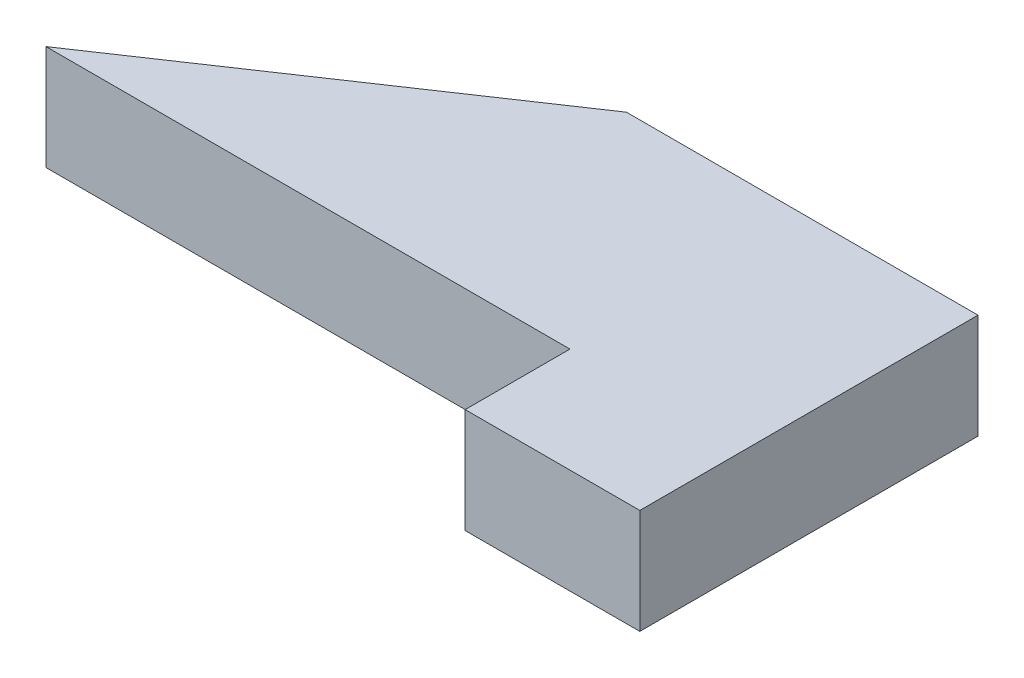
SolidWorks part; units mm, degrees
ref_plane "Front Plane" through (0, 0, 0) normal (0, 0, 1) x (1, 0, 0)
ref_plane "Top Plane" through (0, 0, 0) normal (0, 1, 0) x (1, 0, 0)
ref_plane "Right Plane" through (0, 0, 0) normal (1, 0, 0) x (0, 0, -1)
sketch "Sketch1" plane through (0, 0, 0) normal (0, 1, 0) x (1, 0, 0)
  line L0 (-20, 3) -> (-10.0658, 9.6821)
  line L1 (0, 0) -> (-5, 0)
  line L2 (0, 0) -> (0, 3)
  line L4 (-5, 0) -> (-5, 3)
  line L5 (-5, 3) -> (-20, 3)
  line L6 (0, 3) -> (0, 9.6821)
  line L9 (-10.0658, 9.6821) -> (0, 9.6821)
  dimension "D1" = 5
  dimension "D2" = 3
  dimension "D4" = 20
extrude "Boss-Extrude1" add sketch "Sketch1" along normal blind 3 contours L0 L9 L6 L2 L1 L4 L5
